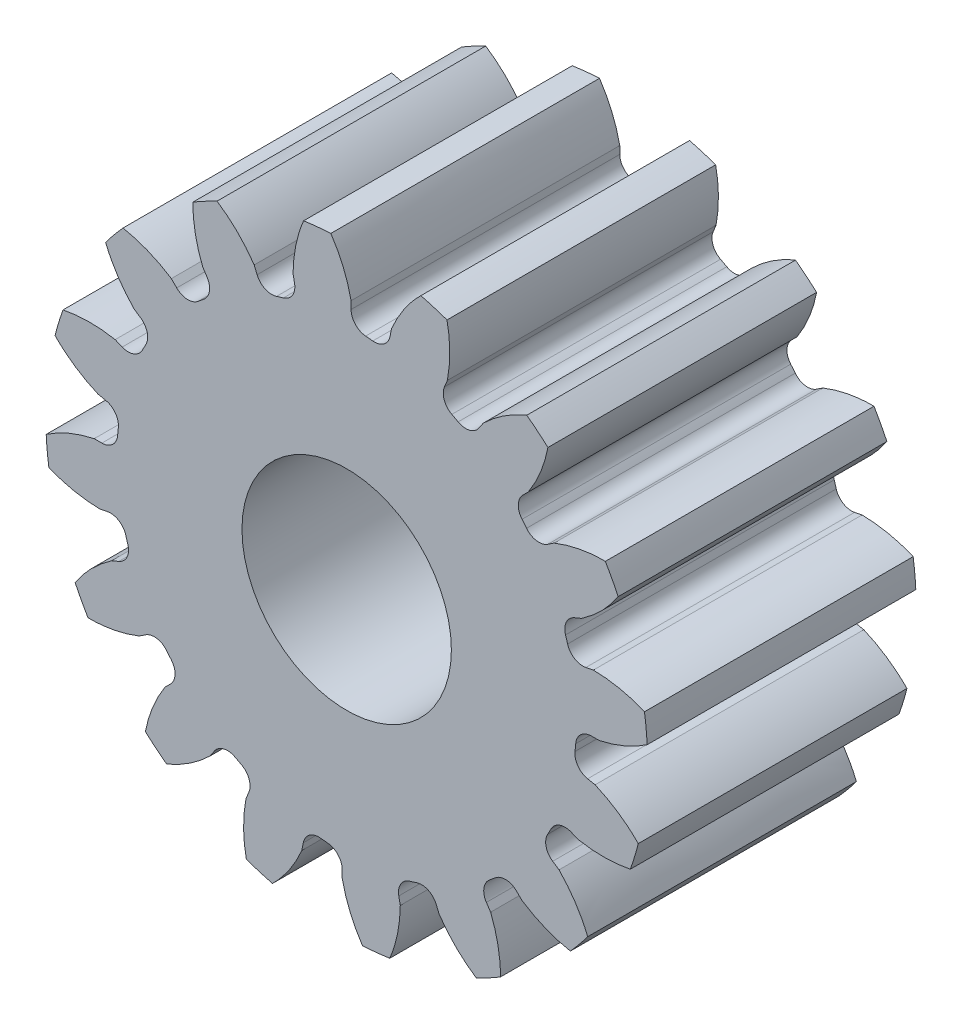
SolidWorks part; units mm, degrees
ref_plane "Front" through (0, 0, 0) normal (0, 0, 1) x (1, 0, 0)
ref_plane "Top" through (0, 0, 0) normal (0, 1, 0) x (1, 0, 0)
ref_plane "Right" through (0, 0, 0) normal (1, 0, 0) x (0, 0, -1)
sketch "Sketch1" plane through (0, 0, 0) normal (0, 0, 1) x (1, 0, 0)
  line L0 (-203.2, 0) -> (203.2, 0) construction
  circle A0 centre (0, 0) radius 7.112
  circle A1 centre (0, 0) radius 6.35 construction
  circle A3 centre (0, 0) radius 5.4316 construction
  dimension "D1" = 0.9184
  dimension "D2" = 1.6804
  dimension "D3" = 0.762
extrude "Boss-Extrude1" add sketch "Sketch1" against normal blind 6.35
sketch "Sketch2" plane through (0, 0, 0) normal (1, 0, 0) x (0, 0, -1)
  line L0 (4.7625, 0) -> (11.1252, 0)
  line L1 (4.7625, 0) -> (4.7625, 5.1594)
  line L2 (4.7625, 5.1594) -> (11.1252, 5.1594)
  line L3 (11.1252, 5.1594) -> (11.1252, 0)
  point P5 (11.1252, -5.1594)
  point P6 (0, -7.112)
  point P7 (6.35, -7.112)
  point P9 (0, 7.112)
sketch "Sketch3" plane through (0, 0, 0) normal (0, 0, 1) x (1, 0, 0)
  line L0 (0, 0) -> (0, 7.112) construction
  line L1 (-2.0409, 5.6072) -> (0, 6.35)
  line L2 (-9.5921, 6.35) -> (9.5921, 6.35) construction
  line L3 (-9.0136, 3.0693) -> (9.0136, 9.6307) construction
  line L4 (-2.0409, 5.6072) -> (0, 0) construction
  line L5 (-4.9755, 3.2939) -> (0, 0) construction
  line L6 (-4.9755, 3.2939) -> (-1.6786, 8.274) construction
  line L7 (-1.4177, 5.7962) -> (0, 0) construction
  line L8 (-1.4177, 5.7962) -> (0.0591, 6.1574) construction
  arc A0 (-2.0409, 5.6072) -> (-4.9755, 3.2939) centre (0, 0) ccw
  circle A1 centre (0, 0) radius 6.35 construction
  circle A2 centre (0, 0) radius 5.967 construction
  arc A3 (-2.0409, 5.6072) -> (-1.4177, 5.7962) centre (0, 0) cw
  circle A4 centre (0, 0) radius 7.112 construction
  point P6 (0, 6.35)
  dimension "D1" = 2.1718
  dimension "Pressure Angle" = 20
  dimension "D2" = 3.8007
  dimension "D3" = 5.9725
  dimension "D4" = 0.6515
  dimension "D5" = 1.5203
sketch "Sketch4" plane through (0, 0, 0) normal (0, 0, 1) x (1, 0, 0)
  line L0 (0, 0) -> (0.6194, 6.289) construction
  line L1 (0.1054, 5.9661) -> (0.1054, 5.4306)
  line L2 (0, 6.35) -> (1.2388, 6.228) construction
  line L3 (1.0605, 5.872) -> (0.9561, 5.3468)
  line L4 (0.1054, 5.4306) -> (0, 0) construction
  line L5 (0, 0) -> (0, 7.112) construction
  line L6 (-4.9755, 3.2939) -> (-1.6786, 8.274) construction
  line L7 (-4.9755, 3.2939) -> (-1.6786, 8.274) construction
  arc A0 (0.9561, 5.3468) -> (0.1054, 5.4306) centre (0, 0) ccw
  arc A1 (0, 6.35) -> (1.2388, 6.228) centre (0, 0) cw construction
  circle A2 centre (0, 0) radius 6.35 construction
  circle A3 centre (0, 0) radius 5.967 construction
  circle A4 centre (0, 0) radius 5.4316 construction
  arc A5 (3.2605, 7.7875) -> (-1.6786, 8.274) centre (0, 0) ccw
  spline S0 degree 2 poles (-1.6786, 8.274) (-0.2007, 7.4121) (0.1054, 5.9661) knots 0 0 0 1 1 1
  spline S1 degree 2 poles (3.2605, 7.7875) (1.6429, 7.2305) (1.0605, 5.872) knots 0 0 0 1 1 1
  dimension "D1" = 1.2468
extrude "Cut-Extrude1" cut sketch "Sketch4" against normal through all
fillet "Fillet1" radius 0.374 2 edges at (0.9561, 5.3468, -3.175) (0.1054, 5.4306, -3.175)
pattern_circular "CirPattern1" count 16 over 360 about axis through (0, 0, -6.35) along (0, 0, 1) of "Cut-Extrude1", "Fillet1"
sketch "Sketch5" plane through (0, 0, 0) normal (0, 0, 1) x (1, 0, 0)
  circle A0 centre (0, 0) radius 2.475
  circle A1 centre (0, 0) radius 2.3813 construction
  dimension "Bore Min" = 4.95
extrude "Cut-Extrude2" cut sketch "Sketch5" against normal through all
sketch "Pitch Dia" plane through (0, 0, 0) normal (0, 0, 1) x (1, 0, 0)
  circle A0 centre (0, 0) radius 6.35 construction
  circle A1 centre (0, 0) radius 6.35 construction
equation "\"D1@Boss-Extrude1\" = \"Face Wd@Sketch2\""
equation "\"D1@Sketch4\" = 1.5708/(\"Number of Teeth@Sketch1\"/\"Ptich Dia@Sketch1\")"
equation "\"D1@CirPattern1\" = \"Number of Teeth@Sketch1\""
equation "\"D1@Fillet1\" = \"D1@Sketch4\"*.3"
equation "\"D1@Sketch1\" = 1.157/(\"Number of Teeth@Sketch1\"/\"Ptich Dia@Sketch1\")"
